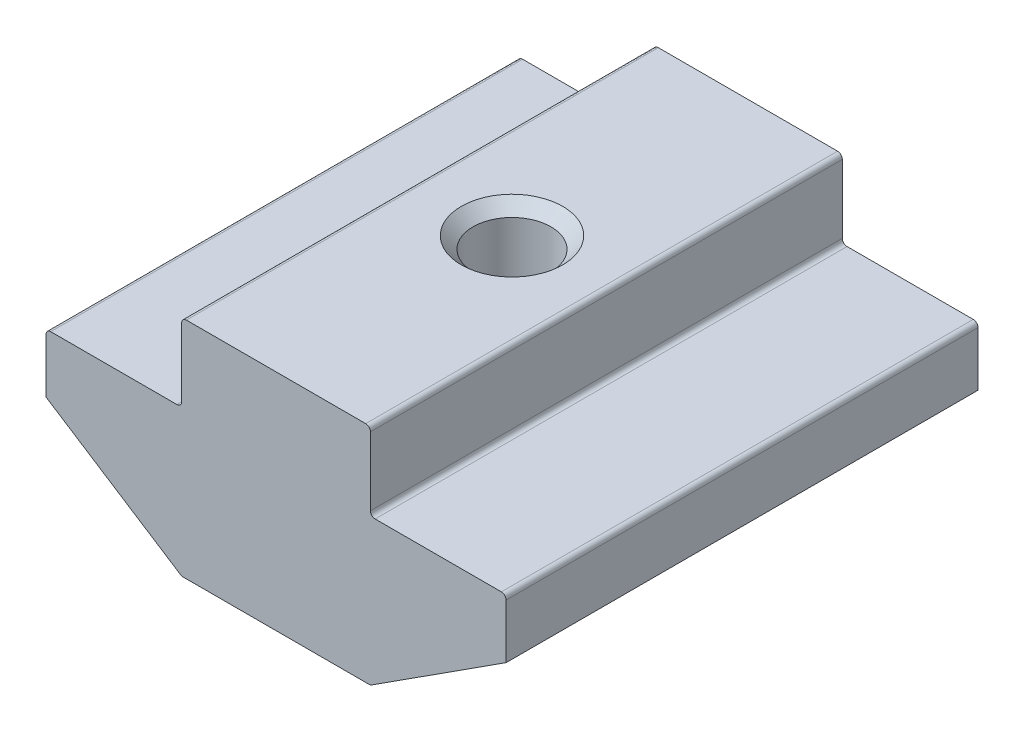
SolidWorks part; units mm, degrees
ref_plane "Спереди" through (0, 0, 0) normal (0, 0, 1) x (1, 0, 0)
ref_plane "Сверху" through (0, 0, 0) normal (0, 1, 0) x (1, 0, 0)
ref_plane "Справа" through (0, 0, 0) normal (1, 0, 0) x (0, 0, -1)
sketch "Эскиз1" plane through (0, 0, 0) normal (0, 0, 1) x (1, 0, 0)
  line L0 (4, 0) -> (-4, 0)
  line L1 (-4, 0) -> (-4, -3.3)
  line L2 (-4, -3.3) -> (-9.75, -3.3)
  line L3 (-9.75, -3.3) -> (-9.75, -5.8)
  line L4 (-9.75, -5.8) -> (-4, -9.5)
  line L5 (-4, -9.5) -> (4, -9.5)
  line L6 (0, -9.5) -> (0, 0) construction
  line L7 (9.75, -5.8) -> (4, -9.5)
  line L8 (9.75, -3.3) -> (9.75, -5.8)
  line L9 (4, -3.3) -> (9.75, -3.3)
  line L10 (4, 0) -> (4, -3.3)
  point P3 (-4, -1.65)
  dimension "D1" = 8
  dimension "D2" = 19.5
  dimension "D3" = 2.5
  dimension "D4" = 9.5
  dimension "D5" = 6.2
extrude "Бобышка-Вытянуть1" add sketch "Эскиз1" along normal mid plane 20
hole_wizard "Отверстие обработанное метчиком M43" positions "Эскиз2" profile "Эскиз4" tap size "M4" standard "ISO" end condition through all
sketch "Эскиз2" plane through (0, 0, 0) normal (0, 1, 0) x (1, 0, 0)
  point P0 (0, 0)
sketch "Эскиз4" plane through (0, 0, 0) normal (1, 0, 0) x (0, 0, 1)
  line L0 (0, 0) -> (0, 9.5)
  line L1 (0, 9.5) -> (2.15, 9.5)
  line L2 (1.65, 9) -> (1.65, 0.5)
  line L3 (1.65, 0.5) -> (2.15, 0)
  line L5 (2.15, 0) -> (0, 0)
  line L6 (-1.65, 0.5) -> (-2.15, 0) construction
  line L7 (2.15, 9.5) -> (1.65, 9)
  line L8 (-2.15, 9.5) -> (-1.65, 9) construction
  line L11 (0, -6.35) -> (0, 107.95) construction
  dimension "Диаметр проходного сверла" = 3.3
  dimension "Глубина проходного сверла" = 9.5
  dimension "Диаметр передней зенковки" = 4.3
  dimension "Угол передней зенковки" = 90
  dimension "Диаметр задней зенковки" = 4.3
  dimension "Угол задней зенковки" = 90
cosmetic thread "Отверстие резьбы1" parameters "D2"=4
fillet "Скругление1" radius 0.2 8 edges at (4, -9.5, 0) (-4, -9.5, 0) (9.75, -3.3, 0) (4, -3.3, 0) (4, 0, 0) (-4, 0, 0) (-9.75, -3.3, 0) (-4, -3.3, 0)
